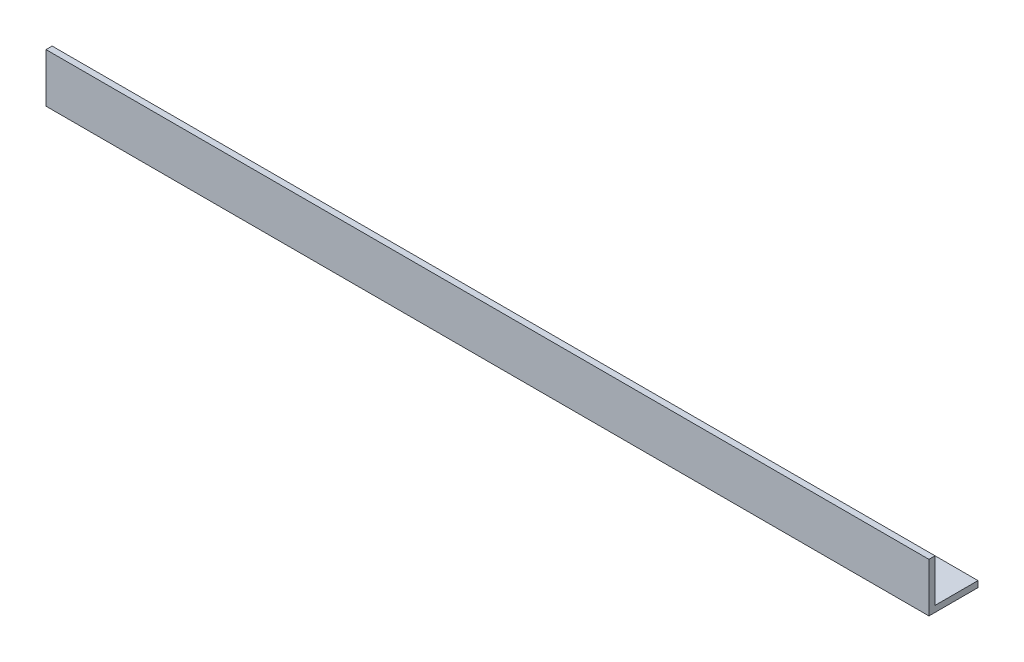
SolidWorks part; units mm, degrees
ref_plane "Front Plane" through (0, 0, 0) normal (0, 0, 1) x (1, 0, 0)
ref_plane "Top Plane" through (0, 0, 0) normal (0, 1, 0) x (1, 0, 0)
ref_plane "Right Plane" through (0, 0, 0) normal (1, 0, 0) x (0, 0, -1)
sketch "Sketch1" plane through (0, 0, 0) normal (1, 0, 0) x (0, 0, -1)
  line L0 (0, 0) -> (0, 25.4)
  line L1 (0, 25.4) -> (3.175, 25.4)
  line L2 (3.175, 25.4) -> (3.175, 3.175)
  line L3 (3.175, 3.175) -> (25.4, 3.175)
  line L4 (25.4, 3.175) -> (25.4, 0)
  line L5 (25.4, 0) -> (0, 0)
  dimension "D1" = 25.4
  dimension "D2" = 3.175
extrude "Boss-Extrude1" add sketch "Sketch1" along normal mid plane 457.2
